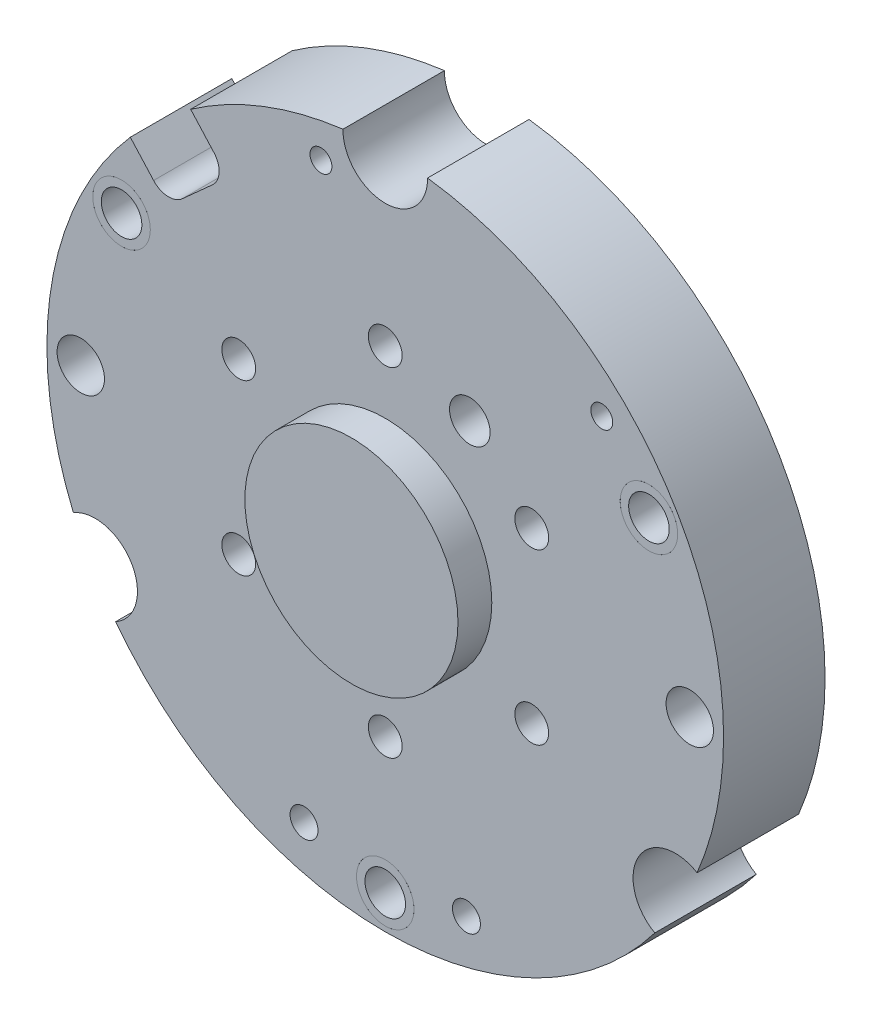
SolidWorks part; units mm, degrees
material "1060-H18"
ref_plane "Piano frontale" through (0, 0, 0) normal (0, 0, 1) x (1, 0, 0)
ref_plane "Piano superiore" through (0, 0, 0) normal (0, 1, 0) x (1, 0, 0)
ref_plane "Piano destro" through (0, 0, 0) normal (1, 0, 0) x (0, 0, -1)
sketch "Schizzo1" plane through (0, 0, 0) normal (0, 0, 1) x (1, 0, 0)
  line L3 (-34.2352, 29.0552) -> (-37.6736, 32.874)
  line L4 (-28.7559, 40.9035) -> (-25.3174, 37.0847)
  line L5 (-25.5395, 32.8479) -> (-29.9984, 28.8331)
  line L6 (-34.2352, 29.0552) -> (-37.6736, 32.874)
  line L7 (-28.7559, 40.9035) -> (-25.3174, 37.0847)
  line L8 (-25.5395, 32.8479) -> (-29.9984, 28.8331)
  arc A2 (32, 30.379) -> (32, 33.621) centre (32, 32) ccw
  arc A3 (32, 33.621) -> (32, 30.379) centre (32, 32) ccw
  arc A4 (32, 30.379) -> (32, 33.621) centre (32, 32) ccw
  arc A5 (32, 33.621) -> (32, 30.379) centre (32, 32) ccw
  arc A6 (-12, -44.067) -> (-12, -39.933) centre (-12, -42) ccw
  arc A7 (-12, -39.933) -> (-12, -44.067) centre (-12, -42) ccw
  arc A8 (-12, -44.067) -> (-12, -39.933) centre (-12, -42) ccw
  arc A9 (-34.2352, 29.0552) -> (-29.9984, 28.8331) centre (-32.0057, 31.0626) ccw
  arc A10 (-37.6736, 32.874) -> (-46.0866, -19.3913) centre (0, 0) ccw
  arc A11 (-39.8377, -30.2151) -> (-46.0866, -19.3913) centre (-42.87, -24.75) ccw
  arc A12 (-39.8377, -30.2151) -> (39.8377, -30.2151) centre (0, 0) ccw
  arc A13 (46.0866, -19.3913) -> (39.8377, -30.2151) centre (42.87, -24.75) ccw
  arc A14 (46.0866, -19.3913) -> (6.2491, 49.608) centre (0, 0) ccw
  arc A15 (-6.2491, 49.608) -> (6.2491, 49.608) centre (0, 49.5) ccw
  arc A16 (-6.2491, 49.608) -> (-28.7559, 40.9035) centre (0, 0) ccw
  arc A17 (-25.5395, 32.8479) -> (-25.3174, 37.0847) centre (-27.5469, 35.0773) ccw
  arc A18 (-34.2352, 29.0552) -> (-29.9984, 28.8331) centre (-32.0057, 31.0626) ccw
  arc A19 (-37.6736, 32.874) -> (-46.0866, -19.3913) centre (0, 0) ccw
  arc A20 (-39.8377, -30.2151) -> (-46.0866, -19.3913) centre (-42.87, -24.75) ccw
  arc A21 (-39.8377, -30.2151) -> (39.8377, -30.2151) centre (0, 0) ccw
  arc A22 (46.0866, -19.3913) -> (39.8377, -30.2151) centre (42.87, -24.75) ccw
  arc A23 (46.0866, -19.3913) -> (6.2491, 49.608) centre (0, 0) ccw
  arc A24 (-6.2491, 49.608) -> (6.2491, 49.608) centre (0, 49.5) ccw
  arc A25 (-6.2491, 49.608) -> (-28.7559, 40.9035) centre (0, 0) ccw
  arc A26 (-25.5395, 32.8479) -> (-25.3174, 37.0847) centre (-27.5469, 35.0773) ccw
  arc A27 (-12, -39.933) -> (-12, -44.067) centre (-12, -42) ccw
  arc A28 (12, -44.067) -> (12, -39.933) centre (12, -42) ccw
  arc A29 (12, -39.933) -> (12, -44.067) centre (12, -42) ccw
  arc A30 (12, -44.067) -> (12, -39.933) centre (12, -42) ccw
  arc A31 (12, -39.933) -> (12, -44.067) centre (12, -42) ccw
  arc A32 (-38.97, 26.75) -> (-38.97, 18.25) centre (-38.97, 22.5) ccw
  arc A33 (-38.97, 18.25) -> (-38.97, 26.75) centre (-38.97, 22.5) ccw
  arc A34 (-38.97, 26.75) -> (-38.97, 18.25) centre (-38.97, 22.5) ccw
  arc A35 (-38.97, 18.25) -> (-38.97, 26.75) centre (-38.97, 22.5) ccw
  arc A36 (38.97, 26.75) -> (38.97, 18.25) centre (38.97, 22.5) ccw
  arc A37 (38.97, 18.25) -> (38.97, 26.75) centre (38.97, 22.5) ccw
  arc A38 (38.97, 26.75) -> (38.97, 18.25) centre (38.97, 22.5) ccw
  arc A39 (38.97, 18.25) -> (38.97, 26.75) centre (38.97, 22.5) ccw
  arc A40 (0, -40.75) -> (0, -49.25) centre (0, -45) ccw
  arc A41 (0, -49.25) -> (0, -40.75) centre (0, -45) ccw
  arc A42 (0, -40.75) -> (0, -49.25) centre (0, -45) ccw
  arc A43 (0, -49.25) -> (0, -40.75) centre (0, -45) ccw
  arc A44 (-45, -3.5) -> (-45, 3.5) centre (-45, 0) ccw
  arc A45 (-45, 3.5) -> (-45, -3.5) centre (-45, 0) ccw
  arc A46 (-45, -3.5) -> (-45, 3.5) centre (-45, 0) ccw
  arc A47 (-45, 3.5) -> (-45, -3.5) centre (-45, 0) ccw
  arc A48 (45, -3.5) -> (45, 3.5) centre (45, 0) ccw
  arc A49 (45, 3.5) -> (45, -3.5) centre (45, 0) ccw
  arc A50 (45, -3.5) -> (45, 3.5) centre (45, 0) ccw
  arc A51 (45, 3.5) -> (45, -3.5) centre (45, 0) ccw
  arc A56 (-9.5, 42.379) -> (-9.5, 45.621) centre (-9.5, 44) ccw
  arc A57 (-9.5, 45.621) -> (-9.5, 42.379) centre (-9.5, 44) ccw
  arc A58 (-9.5, 42.379) -> (-9.5, 45.621) centre (-9.5, 44) ccw
  arc A59 (-9.5, 45.621) -> (-9.5, 42.379) centre (-9.5, 44) ccw
  dimension "D1" = 0
  dimension "D2" = 0
  dimension "D3" = 0
  dimension "D4" = 0
  dimension "D5" = 0
  dimension "D6" = 0
  dimension "D7" = 0
  dimension "D8" = 0
  dimension "D9" = 0
  dimension "D11" = 0
extrude "Estrusione-Estrusione1" add sketch "Schizzo1" along normal blind 15
sketch "Schizzo2" plane through (0, 0, 15) normal (0, 0, 1) x (1, 0, 0)
  arc A2 (-2.1651, -23.75) -> (2.1651, -26.25) centre (0, -25) ccw
  arc A3 (2.1651, -26.25) -> (-2.1651, -23.75) centre (0, -25) ccw
  arc A4 (-2.1651, -23.75) -> (2.1651, -26.25) centre (0, -25) ccw
  arc A5 (2.1651, -26.25) -> (-2.1651, -23.75) centre (0, -25) ccw
  arc A6 (19.4856, -11.25) -> (23.8157, -13.75) centre (21.6506, -12.5) ccw
  arc A7 (23.8157, -13.75) -> (19.4856, -11.25) centre (21.6506, -12.5) ccw
  arc A8 (19.4856, -11.25) -> (23.8157, -13.75) centre (21.6506, -12.5) ccw
  arc A9 (23.8157, -13.75) -> (19.4856, -11.25) centre (21.6506, -12.5) ccw
  arc A10 (19.4856, 13.75) -> (23.8157, 11.25) centre (21.6506, 12.5) ccw
  arc A11 (23.8157, 11.25) -> (19.4856, 13.75) centre (21.6506, 12.5) ccw
  arc A12 (19.4856, 13.75) -> (23.8157, 11.25) centre (21.6506, 12.5) ccw
  arc A13 (23.8157, 11.25) -> (19.4856, 13.75) centre (21.6506, 12.5) ccw
  arc A14 (9.9019, 23.1506) -> (15.0981, 20.1506) centre (12.5, 21.6506) ccw
  arc A15 (15.0981, 20.1506) -> (9.9019, 23.1506) centre (12.5, 21.6506) ccw
  arc A16 (9.9019, 23.1506) -> (15.0981, 20.1506) centre (12.5, 21.6506) ccw
  arc A17 (15.0981, 20.1506) -> (9.9019, 23.1506) centre (12.5, 21.6506) ccw
  arc A22 (-23.8157, -11.25) -> (-19.4856, -13.75) centre (-21.6506, -12.5) ccw
  arc A23 (-19.4856, -13.75) -> (-23.8157, -11.25) centre (-21.6506, -12.5) ccw
  arc A24 (-23.8157, -11.25) -> (-19.4856, -13.75) centre (-21.6506, -12.5) ccw
  arc A25 (-19.4856, -13.75) -> (-23.8157, -11.25) centre (-21.6506, -12.5) ccw
  arc A26 (-2.1651, 26.25) -> (2.1651, 23.75) centre (0, 25) ccw
  arc A27 (2.1651, 23.75) -> (-2.1651, 26.25) centre (0, 25) ccw
  arc A28 (-2.1651, 26.25) -> (2.1651, 23.75) centre (0, 25) ccw
  arc A29 (2.1651, 23.75) -> (-2.1651, 26.25) centre (0, 25) ccw
  arc A30 (-23.8157, 13.75) -> (-19.4856, 11.25) centre (-21.6506, 12.5) ccw
  arc A31 (-19.4856, 11.25) -> (-23.8157, 13.75) centre (-21.6506, 12.5) ccw
  arc A32 (-23.8157, 13.75) -> (-19.4856, 11.25) centre (-21.6506, 12.5) ccw
  arc A33 (-19.4856, 11.25) -> (-23.8157, 13.75) centre (-21.6506, 12.5) ccw
  dimension "D1" = 0
  dimension "D2" = 0
  dimension "D3" = 0
  dimension "D4" = 0
  dimension "D6" = 0
  dimension "D7" = 0
  dimension "D8" = 0
extrude "Taglio-Estrusione1" cut sketch "Schizzo2" against normal blind 15
sketch "Schizzo3" plane through (0, 0, 0) normal (0, 0, -1) x (-1, 0, 0)
  circle A74 centre (0, 25) radius 5.5
  circle A75 centre (0, 25) radius 5.5
  circle A85 centre (21.6506, 12.5) radius 5.5
  circle A86 centre (21.6506, -12.5) radius 5.5
  circle A87 centre (0, -25) radius 5.5
  circle A88 centre (-21.6506, -12.5) radius 5.5
  circle A89 centre (-21.6506, 12.5) radius 5.5
  dimension "D1" = 3
extrude "Taglio-Estrusione2" cut sketch "Schizzo3" against normal blind 5
sketch "Schizzo5" plane through (0, 0, 15) normal (0, 0, 1) x (1, 0, 0)
  arc A2 (13.6399, -7.875) -> (-13.6399, 7.875) centre (0, 0) ccw
  arc A3 (-13.6399, 7.875) -> (13.6399, -7.875) centre (0, 0) ccw
  arc A6 (13.6399, -7.875) -> (-13.6399, 7.875) centre (0, 0) ccw
  arc A7 (-13.6399, 7.875) -> (13.6399, -7.875) centre (0, 0) ccw
  dimension "D1" = 0
extrude "Estrusione-Estrusione2" add sketch "Schizzo5" along normal blind 5 separate body contours A7 A6
sketch "Schizzo6" plane through (0, 0, 0) normal (0, 0, -1) x (-1, 0, 0)
  circle A0 centre (0, 0) radius 35
extrude "Taglio-Estrusione3" cut sketch "Schizzo6" against normal blind 0.3
sketch "Schizzo7" plane through (0, 0, 0) normal (0, 0, -1) x (-1, 0, 0)
  circle A0 centre (38.97, 22.5) radius 3
  circle A1 centre (0, -44.998) radius 3
  circle A2 centre (-38.97, 22.5) radius 3
  circle A3 centre (38.97, 22.5) radius 4.25 construction
  circle A4 centre (0, -45) radius 4.25 construction
  circle A5 centre (-38.97, 22.5) radius 4.25 construction
  circle A6 centre (38.97, 22.5) radius 4.25
  circle A7 centre (0, -45) radius 4.25
  circle A8 centre (-38.97, 22.5) radius 4.25
  point P10 (0, 0.0007)
  dimension "D1" = 6
  dimension "D2" = 3
extrude "Estrusione-Estrusione3" add sketch "Schizzo7" against normal blind 15 separate body
